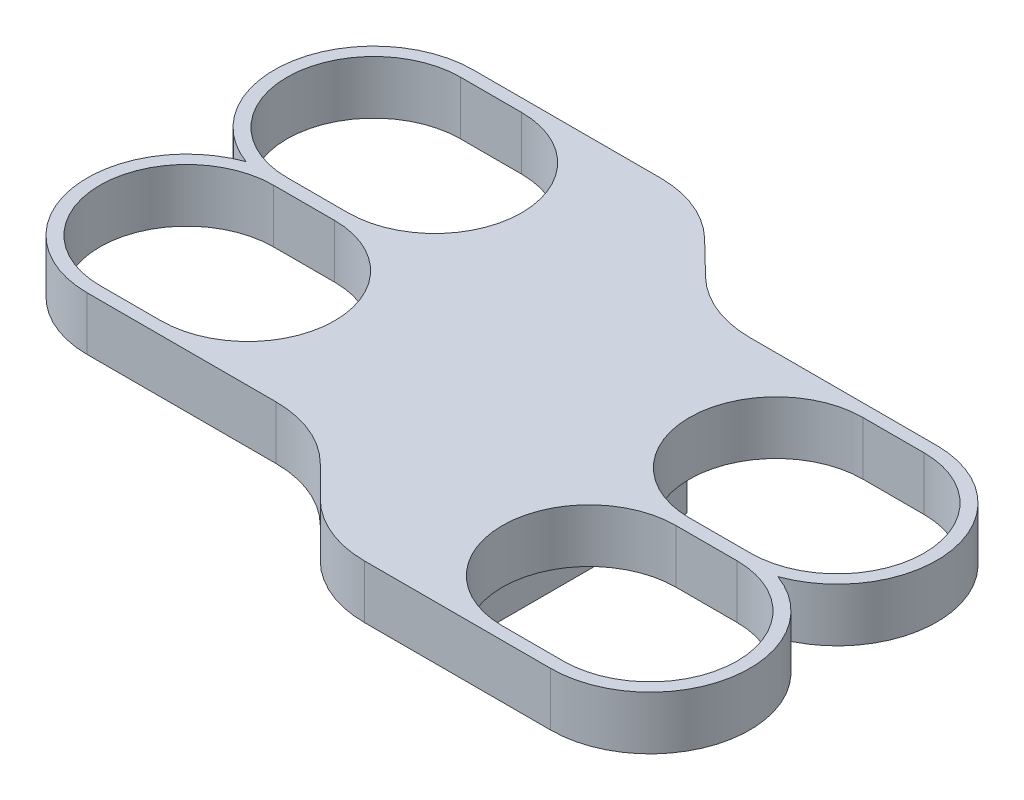
SolidWorks part; units mm, degrees
ref_plane "Front Plane" through (0, 0, 0) normal (0, 0, 1) x (1, 0, 0)
ref_plane "Top Plane" through (0, 0, 0) normal (0, 1, 0) x (1, 0, 0)
ref_plane "Right Plane" through (0, 0, 0) normal (1, 0, 0) x (0, 0, -1)
sketch "Sketch1" plane through (0, 0, 0) normal (0, 1, 0) x (1, 0, 0)
  line L0 (-46.4, 26.25) -> (0, 26.25) construction
  line L1 (-46.4, -8.75) -> (0, -8.75) construction
  line L2 (0, 8.75) -> (46.4, 8.75) construction
  line L3 (0, -26.25) -> (46.4, -26.25) construction
  line L4 (0, -8.75) -> (0, 8.75) construction
  line L5 (-40.6829, 26.25) -> (-52.1171, 26.25) construction
  line L6 (-40.6829, 10) -> (-52.1171, 10)
  line L7 (-40.6829, 42.5) -> (-52.1171, 42.5)
  line L8 (-40.6829, 26.25) -> (-52.1171, 26.25) construction
  line L9 (-40.6829, 7.6233) -> (-52.1171, 7.6233)
  line L10 (-40.6829, 44.8767) -> (-52.1171, 44.8767)
  line L11 (-40.6829, -8.75) -> (-52.1171, -8.75) construction
  line L12 (-40.6829, 7.5) -> (-52.1171, 7.5)
  line L13 (-40.6829, -25) -> (-52.1171, -25)
  line L14 (-40.6829, -8.75) -> (-52.1171, -8.75) construction
  line L15 (-40.6829, 9.8767) -> (-52.1171, 9.8767)
  line L16 (-40.6829, -27.3767) -> (-52.1171, -27.3767)
  line L17 (-8.4995, 0) -> (8.4995, 0) construction
  line L20 (-40.6829, 44.8767) -> (-17.1199, 44.8767)
  line L23 (-3.1788, 39.217) -> (3.1788, 33.0364)
  line L26 (17.1199, 27.3767) -> (40.6829, 27.3767)
  line L29 (40.6829, -44.8767) -> (17.2848, -44.8767)
  line L30 (40.6829, -26.25) -> (52.1171, -26.25) construction
  line L31 (40.6829, -10) -> (52.1171, -10)
  line L32 (40.6829, -42.5) -> (52.1171, -42.5)
  line L33 (40.6829, -26.25) -> (52.1171, -26.25) construction
  line L34 (40.6829, -7.6233) -> (52.1171, -7.6233)
  line L35 (40.6829, -44.8767) -> (52.1171, -44.8767)
  line L36 (40.6829, 8.75) -> (52.1171, 8.75) construction
  line L37 (40.6829, -7.5) -> (52.1171, -7.5)
  line L38 (40.6829, 25) -> (52.1171, 25)
  line L39 (40.6829, 8.75) -> (52.1171, 8.75) construction
  line L40 (40.6829, -9.8767) -> (52.1171, -9.8767)
  line L41 (40.6829, 27.3767) -> (52.1171, 27.3767)
  line L42 (3.1427, -39.0188) -> (-2.6416, -33.2346)
  line L43 (-16.7837, -27.3767) -> (-40.6829, -27.3767)
  circle A0 centre (-46.4, 26.25) radius 15.75 construction
  circle A1 centre (46.4, 8.75) radius 15.75 construction
  circle A2 centre (-46.4, -8.75) radius 15.75 construction
  circle A3 centre (46.4, -26.25) radius 15.75 construction
  arc A4 (-40.6829, 10) -> (-40.6829, 42.5) centre (-40.6829, 26.25) ccw
  arc A5 (-52.1171, 42.5) -> (-52.1171, 10) centre (-52.1171, 26.25) ccw
  arc A7 (-52.1171, 44.8767) -> (-58.497, 8.75) centre (-52.1171, 26.25) ccw
  arc A8 (-40.6829, 7.5) -> (-40.6829, -25) centre (-40.6829, -8.75) cw
  arc A9 (-52.1171, -25) -> (-52.1171, 7.5) centre (-52.1171, -8.75) cw
  arc A11 (-52.1171, -27.3767) -> (-58.497, 8.75) centre (-52.1171, -8.75) cw
  arc A20 (40.6829, -10) -> (40.6829, -42.5) centre (40.6829, -26.25) ccw
  arc A21 (52.1171, -42.5) -> (52.1171, -10) centre (52.1171, -26.25) ccw
  arc A23 (52.1171, -44.8767) -> (58.497, -8.75) centre (52.1171, -26.25) ccw
  arc A24 (40.6829, -7.5) -> (40.6829, 25) centre (40.6829, 8.75) cw
  arc A25 (52.1171, 25) -> (52.1171, -7.5) centre (52.1171, 8.75) cw
  arc A27 (52.1171, 27.3767) -> (58.497, -8.75) centre (52.1171, 8.75) cw
  arc A28 (17.2848, -44.8767) -> (3.1427, -39.0188) centre (17.2848, -24.8767) cw
  arc A29 (-2.6416, -33.2346) -> (-16.7837, -27.3767) centre (-16.7837, -47.3767) ccw
  arc A30 (3.1788, 33.0364) -> (17.1199, 27.3767) centre (17.1199, 47.3767) ccw
  arc A31 (-17.1199, 44.8767) -> (-3.1788, 39.217) centre (-17.1199, 24.8767) cw
  point P8 (0, 0)
  point P14 (-46.4, 26.25)
  point P23 (-46.4, 26.25)
  point P30 (-46.4, -8.75)
  point P37 (-46.4, -8.75)
  point P44 (0, 0)
  point P57 (-8.4995, -27.3767)
  point P74 (46.4, -26.25)
  point P81 (46.4, -26.25)
  point P88 (46.4, 8.75)
  point P95 (46.4, 8.75)
  dimension "D5" = 31.5
  dimension "D7" = 20
  dimension "D1" = 17.5
  dimension "D2" = 17.5
  dimension "D3" = 17.5
  dimension "D4" = 46.4
  dimension "D6" = 32.5
extrude "Boss-Extrude1" add sketch "Sketch1" along normal blind 10
sketch "Sketch2" plane through (0, 10, 0) normal (0, 1, 0) x (1, 0, 0)
  line L0 (-12.7, -20) -> (-12.7, 20)
  line L1 (-12.7, -20) -> (12.7, -20)
  line L2 (-12.7, 20) -> (12.7, 20)
  line L3 (12.7, -20) -> (12.7, 20)
  line L4 (-12.7, -20) -> (12.7, 20) construction
  line L5 (-12.7, 20) -> (12.7, -20) construction
  point P1 (0, 0)
  dimension "D1" = 25.4
  dimension "D2" = 40
extrude "Boss-Extrude3" add sketch "Sketch2" against normal blind 17 from surface at -10 starting at face at (0.0716, 0, 0)
fillet "Fillet2" radius 5 4 edges at (12.7, 0, 0) (0, 0, 20) (0, 0, -20) (-12.7, 0, 0)
